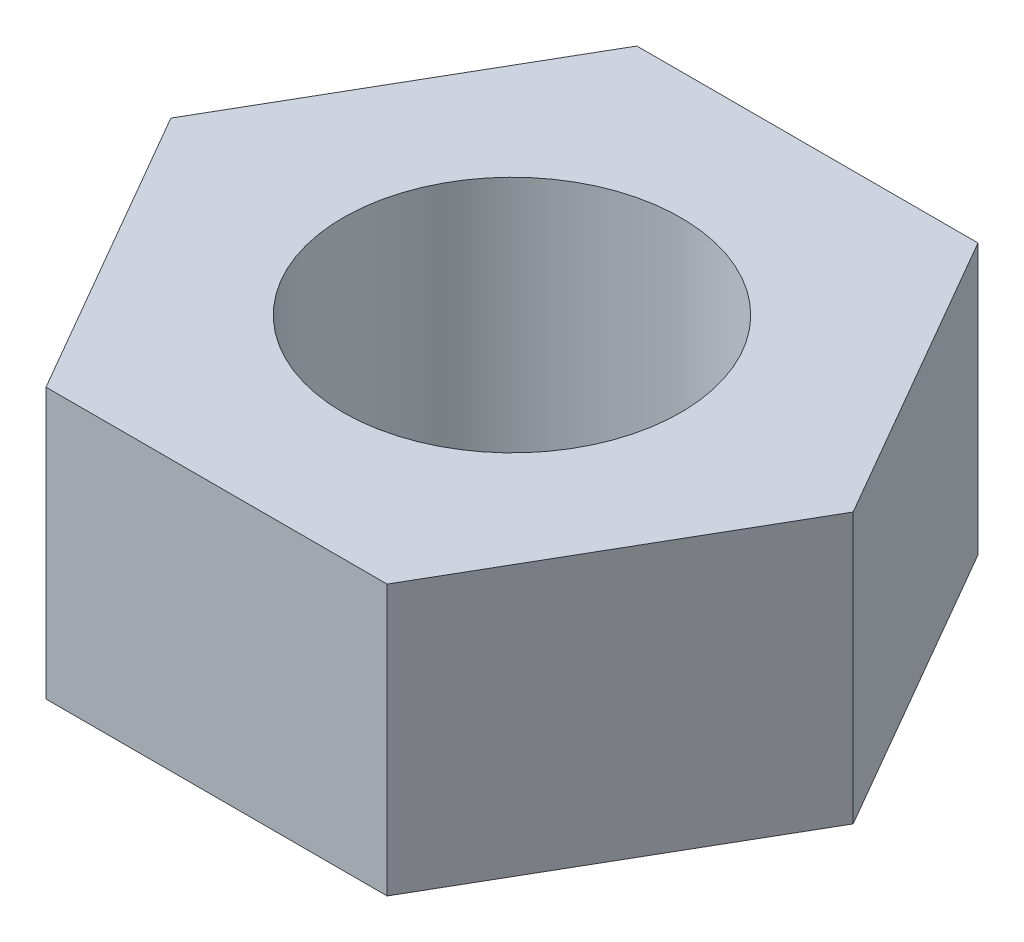
SolidWorks part; units mm, degrees
ref_plane "Front Plane" through (0, 0, 0) normal (0, 0, 1) x (1, 0, 0)
ref_plane "Top Plane" through (0, 0, 0) normal (0, 1, 0) x (1, 0, 0)
ref_plane "Right Plane" through (0, 0, 0) normal (1, 0, 0) x (0, 0, -1)
sketch "Sketch1" plane through (0, 0, 0) normal (0, 1, 0) x (1, 0, 0)
  line L1 (4.0415, 0) -> (2.0207, 3.5)
  line L2 (2.0207, 3.5) -> (-2.0207, 3.5)
  line L3 (-2.0207, 3.5) -> (-4.0415, 0)
  line L4 (-4.0415, 0) -> (-2.0207, -3.5)
  line L5 (-2.0207, -3.5) -> (2.0207, -3.5)
  line L6 (2.0207, -3.5) -> (4.0415, 0)
  circle A0 centre (0, 0) radius 3.5 construction
  circle A1 centre (0, 0) radius 2
  dimension "D1" = 4
  dimension "D2" = 7
extrude "Boss-Extrude1" add sketch "Sketch1" along normal blind 3.2
